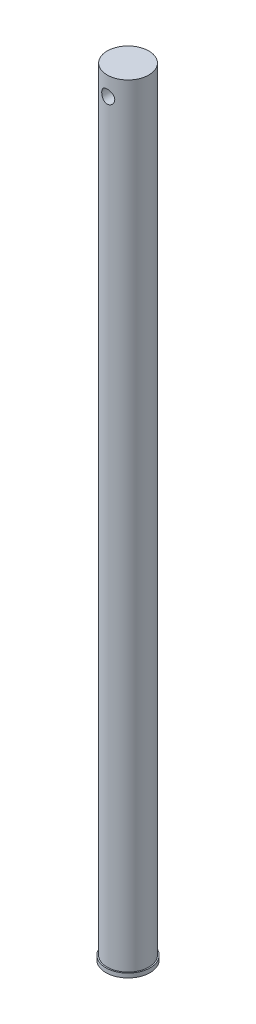
SolidWorks part; units mm, degrees
material "AISI 1020"
ref_plane "Alzado" through (0, 0, 0) normal (0, 0, 1) x (1, 0, 0)
ref_plane "Planta" through (0, 0, 0) normal (0, 1, 0) x (1, 0, 0)
ref_plane "Vista lateral" through (0, 0, 0) normal (1, 0, 0) x (0, 0, -1)
sketch "Croquis1" plane through (0, 0, 0) normal (0, 1, 0) x (1, 0, 0)
  circle A0 centre (0, 0) radius 9.906
  dimension "D1" = 19.812
extrude "Saliente-Extruir1" add sketch "Croquis1" along normal blind 367.538
sketch "Croquis2" plane through (0, 0, 0) normal (0, 0, 1) x (1, 0, 0)
  line L0 (9.906, 367.538) -> (-9.906, 367.538) construction
  circle A0 centre (0, 358.648) radius 3.1
  dimension "D1" = 6.2
  dimension "D2" = 8.89
extrude "Cortar-Extruir1" cut sketch "Croquis2" against normal mid plane 20
sketch "Croquis3" plane through (0, 0, 0) normal (0, -1, 0) x (1, 0, 0)
  circle A0 centre (0, 0) radius 10.5
extrude "Saliente-Extruir2" add sketch "Croquis3" along normal blind 2
